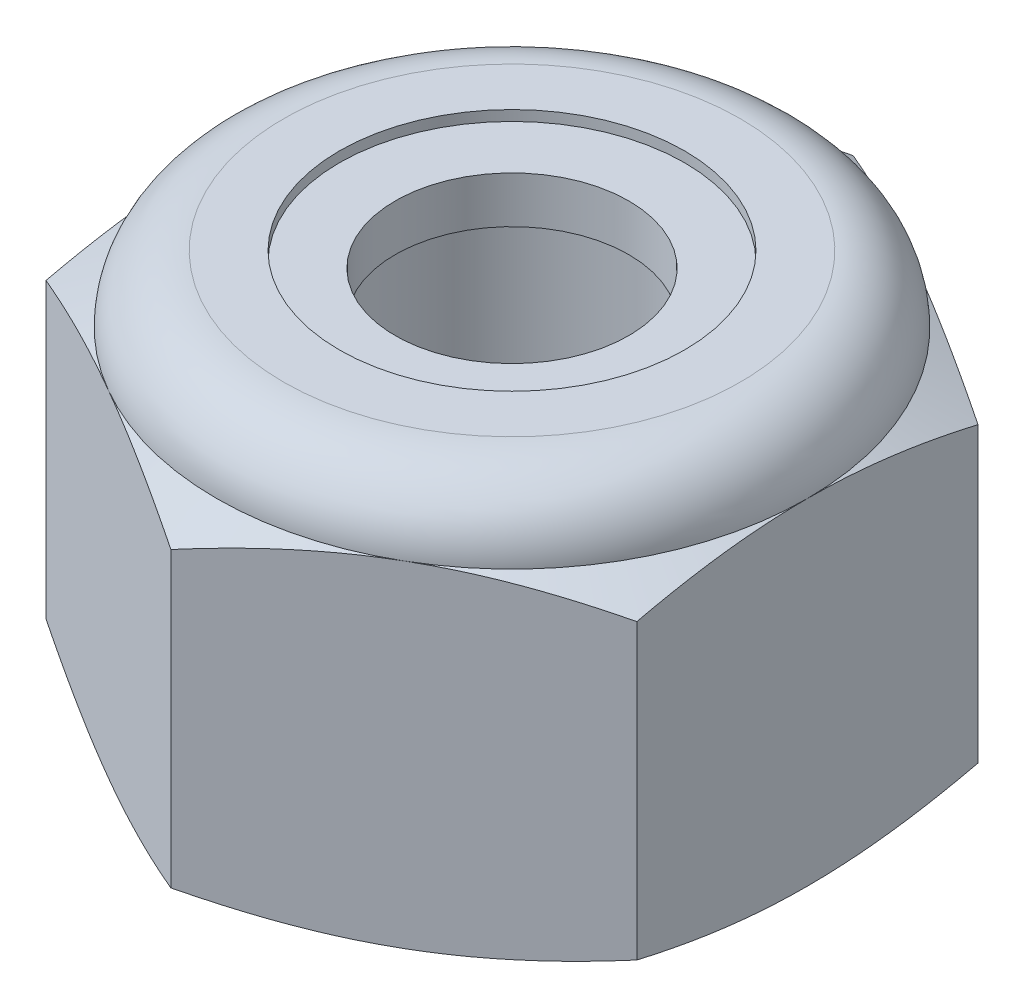
SolidWorks part; units mm, degrees
ref_plane "Front" through (0, 0, 0) normal (0, 0, 1) x (1, 0, 0)
ref_plane "Top" through (0, 0, 0) normal (0, 1, 0) x (1, 0, 0)
ref_plane "Right" through (0, 0, 0) normal (1, 0, 0) x (0, 0, -1)
sketch "Sketch1" plane through (0, 0, 0) normal (0, 1, 0) x (1, 0, 0)
  line L1 (0, 5.041) -> (-4.3656, 2.5205)
  line L2 (-4.3656, 2.5205) -> (-4.3656, -2.5205)
  line L3 (-4.3656, -2.5205) -> (0, -5.041)
  line L4 (0, -5.041) -> (4.3656, -2.5205)
  line L5 (4.3656, -2.5205) -> (4.3656, 2.5205)
  line L6 (4.3656, 2.5205) -> (0, 5.041)
  circle A0 centre (0, 0) radius 4.3656 construction
  dimension "Hex Flats" = 8.7312
extrude "Extrude1" add sketch "Sketch1" along normal blind 5.9531
sketch "Sketch2" plane through (0, 0, 0) normal (1, 0, 0) x (0, 0, -1)
  line L0 (-2.0828, 0) -> (-2.0828, 5.9531) construction
  line L1 (0, 0) -> (2.0828, 0)
  line L2 (0, 0) -> (0, 5.9531)
  line L3 (0, 5.9531) -> (2.0828, 5.9531)
  line L4 (2.0828, 0) -> (2.0828, 5.9531)
  line L5 (-2.5205, 5.9531) -> (2.5205, 5.9531) construction
  line L7 (0, -2.0828) -> (0, 0) construction
  dimension "Thread Dia" = 4.1656
revolve "Revolve1" add sketch "Sketch2" angle 360 about L7
sketch "Sketch3" plane through (0, 0, 0) normal (1, 0, 0) x (0, 0, -1)
  line L0 (2.0828, 5.9531) -> (-2.0828, 5.9531) construction
  line L1 (-2.0828, 5.9531) -> (-2.0828, 5.1594) construction
  line L2 (-2.0828, 5.1594) -> (2.0828, 5.9531) construction
  line L3 (2.0828, 5.9531) -> (2.1014, 5.8557) construction
  line L4 (2.1014, 5.8557) -> (2.2314, 5.1734)
  line L5 (2.2314, 5.1734) -> (1.7629, 5.3366)
  line L6 (1.7629, 5.3366) -> (1.7258, 5.5316)
  line L7 (1.7258, 5.5316) -> (2.1014, 5.8557)
  line L8 (1.7443, 5.4341) -> (2.1664, 5.5145) construction
  line L9 (2.0828, 5.9531) -> (2.0828, 5.4986) construction
  line L10 (2.0828, 5.4986) -> (-2.0828, 4.7049) construction
  line L11 (-2.0828, 4.7049) -> (-2.0828, 5.1594) construction
  line L12 (-0.1622, 5.9531) -> (0.1622, 4.2503) construction
  line L13 (-2.0828, 0) -> (-2.0828, 5.9531) construction
  line L14 (0, 5.9531) -> (2.0828, 5.9531) construction
  line L15 (2.0828, 0) -> (2.0828, 5.9531) construction
  point P13 (0, 5.1017)
  dimension "D1" = 0.0992
  dimension "D2" = 0.1984
  dimension "Thread Pitch" = 0.7937
  dimension "D4" = 60
  dimension "D5" = 0.7937
revolve "Cut-Revolve1" [suppressed] cut sketch "Sketch3" angle 360 about L12
pattern_linear "LPattern1" [suppressed] count 8 spacing 0.7937 along (0, 1, 0) count 2 spacing 0.7937 along (0, 1, 0)
sketch "Sketch4" plane through (0, 0, 0) normal (1, 0, 0) x (0, 0, -1)
  line L0 (0, 5.9531) -> (2.0828, 5.9531)
  line L1 (2.0828, 5.9531) -> (1.7258, 5.7866)
  line L2 (1.7258, 5.7866) -> (1.7258, 0.1665)
  line L3 (1.7258, 0.1665) -> (2.0828, 0)
  line L4 (2.0828, 0) -> (0, 0)
  line L5 (0, 0) -> (0, 5.9531)
  line L6 (2.0828, 0) -> (2.0828, 5.9531) construction
  line L7 (0, 5.9531) -> (2.0828, 5.9531) construction
  line L8 (0, 0) -> (2.0828, 0) construction
  line L9 (0, 0) -> (0, 5.9531) construction
  line L10 (0, 5.9531) -> (0, 6.3471) construction
  dimension "D1" = 25
revolve "Cut-Revolve2" cut sketch "Sketch4" angle 360 about L10
combine bodies "Combine1" operation type subtract main body 112 bodies to subtract 109
sketch "Sketch5" plane through (0, 0, 0) normal (1, 0, 0) x (0, 0, -1)
  line L0 (0, 0) -> (4.3656, 0)
  line L1 (4.3656, 0) -> (5.041, 0.3149)
  line L2 (5.041, 0.3149) -> (5.041, 4.646)
  line L3 (5.041, 4.646) -> (4.3656, 4.9609)
  line L4 (3.3734, 5.9531) -> (3.3734, 7.2231)
  line L5 (3.3734, 7.2231) -> (6.311, 7.2231)
  line L6 (6.311, 7.2231) -> (6.311, -1.27)
  line L7 (6.311, -1.27) -> (0, -1.27)
  line L8 (0, -1.27) -> (0, 0)
  line L9 (4.3656, 4.9609) -> (4.3656, 0) construction
  line L10 (0, 0) -> (2.0828, 0) construction
  line L13 (5.041, 2.4805) -> (6.311, 2.4805) construction
  line L14 (5.041, 5.9531) -> (5.041, 0) construction
  line L15 (0, 0) -> (0, 7.2231) construction
  line L20 (0, 7.2231) -> (3.3734, 7.2231) construction
  line L22 (0, 5.9531) -> (2.0828, 5.9531) construction
  arc A0 (4.3656, 4.9609) -> (3.3734, 5.9531) centre (3.3734, 4.9609) ccw
  dimension "D1" = 25
  dimension "D2" = 1.27
  dimension "D3" = 5.9531
  dimension "D4" = 0.9922
revolve "Cut-Revolve3" cut sketch "Sketch5" angle 360 about L15
sketch "Sketch6" plane through (0, 0, 0) normal (1, 0, 0) x (0, 0, -1)
  line L0 (0, 4.9609) -> (4.2132, 4.9609)
  line L1 (3.3734, 5.8007) -> (2.5496, 5.8007)
  line L2 (0, 7.2231) -> (0, 4.9609)
  line L3 (2.5496, 7.2231) -> (0, 7.2231)
  line L4 (0, 7.2231) -> (3.3734, 7.2231) construction
  line L5 (0, 0) -> (0, 7.2231) construction
  line L6 (0, 7.2231) -> (0, 44.323) construction
  line L7 (2.5496, 5.8007) -> (2.5496, 7.2231)
  line L8 (3.3734, 5.9531) -> (3.3734, 5.8007) construction
  line L9 (2.5496, 5.8007) -> (1.7258, 5.8007) construction
  line L10 (1.7258, 5.8007) -> (1.7258, 5.7866) construction
  arc A0 (4.2132, 4.9609) -> (3.3734, 5.8007) centre (3.3734, 4.9609) ccw
  arc A1 (4.3656, 4.9609) -> (3.3734, 5.9531) centre (3.3734, 4.9609) ccw construction
  dimension "D1" = 0.1524
revolve "Cut-Revolve4" cut sketch "Sketch6" angle 360 about L6
sketch "Sketch7" plane through (0, 0, 0) normal (1, 0, 0) x (0, 0, -1)
  line L0 (1.7258, 5.0371) -> (4.1332, 5.0371)
  line L1 (3.3734, 5.7245) -> (1.7258, 5.7245)
  line L2 (1.7258, 5.7245) -> (1.7258, 5.0371)
  line L3 (1.7258, 5.0371) -> (0, 5.0371) construction
  line L4 (0, 5.0371) -> (0, 5.7245) construction
  line L5 (0, 5.7245) -> (1.7258, 5.7245) construction
  line L6 (1.7258, 5.0371) -> (1.7258, 4.9609) construction
  line L7 (0, 4.9609) -> (4.2132, 4.9609) construction
  line L8 (3.3734, 5.7245) -> (3.3734, 5.8007) construction
  arc A0 (4.1332, 5.0371) -> (3.3734, 5.7245) centre (3.3734, 4.9609) ccw
  arc A2 (4.2132, 4.9609) -> (3.3734, 5.8007) centre (3.3734, 4.9609) ccw construction
  dimension "D1" = 0.0762
revolve "Revolve2" add sketch "Sketch7" angle 360 about L4
equation "\"D1@Sketch3\"=\"Thread Pitch@Sketch3\"/8"
equation "\"D2@Sketch3\"=\"Thread Pitch@Sketch3\"/4"
equation "\"D5@Sketch3\"=\"Thread Pitch@Sketch3\""
equation "\"D4@LPattern1\"=\"Thread Pitch@Sketch3\""
equation "\"D3@LPattern1\"=\"Thread Pitch@Sketch3\""
equation "\"D1@LPattern1\"=\"Height@Extrude1\"/\"Thread Pitch@Sketch3\""
equation "\"D4@Sketch5\"=\"Height@Extrude1\"/6"
